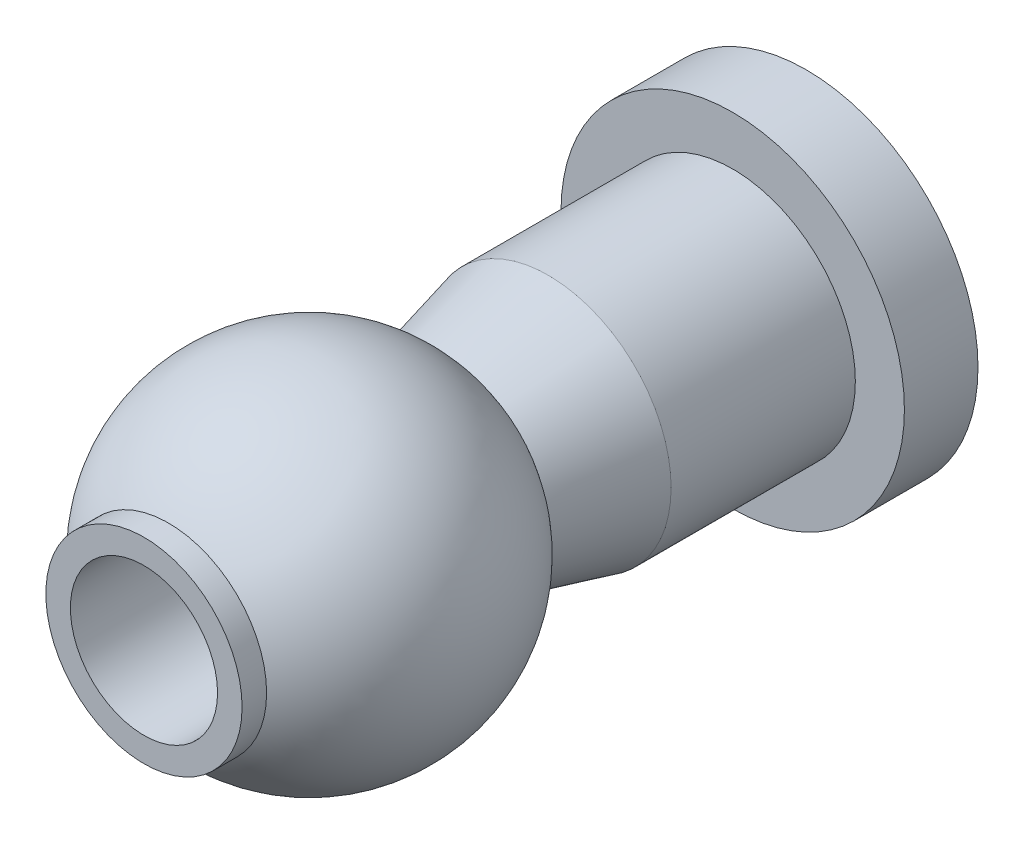
SolidWorks part; units mm, degrees
material "1060 Alloy"
ref_plane "Front Plane" through (0, 0, 0) normal (0, 0, 1) x (1, 0, 0)
ref_plane "Top Plane" through (0, 0, 0) normal (0, 1, 0) x (1, 0, 0)
ref_plane "Right Plane" through (0, 0, 0) normal (1, 0, 0) x (0, 0, -1)
sketch "Sketch1" plane through (0, 0, 0) normal (1, 0, 0) x (0, 0, -1)
  line L0 (0, 0) -> (13.5, 0) construction
  line L1 (6.2446, 2) -> (8.2446, 2.5)
  line L2 (8.2446, 2.5) -> (12, 2.5)
  line L3 (12, 2.5) -> (12, 3.5)
  line L4 (12, 3.5) -> (13.5, 3.5)
  line L5 (13.5, 3.5) -> (13.5, 1.5)
  line L6 (13.5, 1.5) -> (0, 1.5)
  line L7 (0, 1.5) -> (0, 2)
  line L8 (0, 2) -> (0.5, 2)
  arc A1 (6.2446, 2) -> (0.5, 2) centre (3.3723, 0) ccw
  dimension "D10" = 3.5
  dimension "D1" = 3.5
  dimension "D2" = 2.5
  dimension "D3" = 2
  dimension "D4" = 1.5
  dimension "D5" = 13.5
  dimension "D6" = 0
  dimension "D7" = 1.5
  dimension "D8" = 2
  dimension "D9" = 2
  dimension "D11" = 0.5
revolve "Revolve1" add sketch "Sketch1" angle 360 about L0
